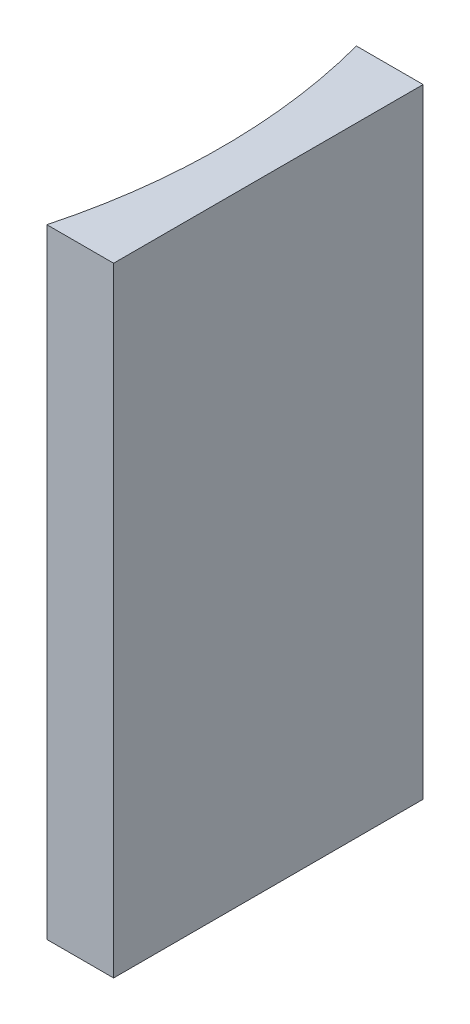
SolidWorks part; units mm, degrees
ref_plane "前视基准面" through (0, 0, 0) normal (0, 0, 1) x (1, 0, 0)
ref_plane "上视基准面" through (0, 0, 0) normal (0, 1, 0) x (1, 0, 0)
ref_plane "右视基准面" through (0, 0, 0) normal (1, 0, 0) x (0, 0, -1)
sketch "草图1" plane through (0, 0, 0) normal (0, 1, 0) x (1, 0, 0)
  line L0 (0, 0) -> (0, -20)
  line L1 (0, 0) -> (-4.3115, 0)
  line L2 (0, -20) -> (-4.3115, -20)
  line L3 (8.2336, -10) -> (-10.4405, -10) construction
  arc A0 (-4.3115, -20) -> (-4.3115, 0) centre (-41.78, -10) ccw
  point P7 (-3, -10)
  point P8 (0, -10)
  dimension "D2" = 38.78
  dimension "D3" = 3
  dimension "D1" = 20
extrude "凸台-拉伸1" add sketch "草图1" along normal blind 40
